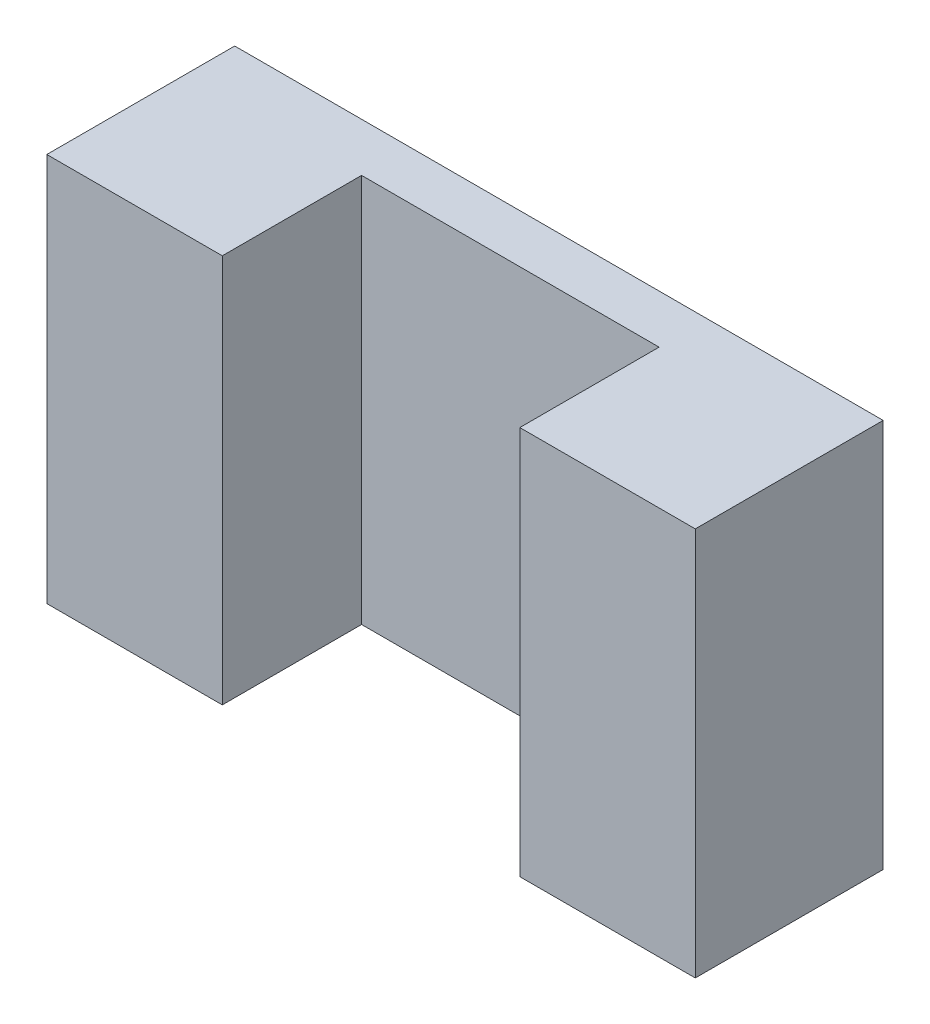
SolidWorks part; units mm, degrees
material "ABS"
ref_plane "Front Plane" through (0, 0, 0) normal (0, 0, 1) x (1, 0, 0)
ref_plane "Top Plane" through (0, 0, 0) normal (0, 1, 0) x (1, 0, 0)
ref_plane "Right Plane" through (0, 0, 0) normal (1, 0, 0) x (0, 0, -1)
sketch "Sketch1" plane through (0, 0, 0) normal (0, 0, 1) x (1, 0, 0)
  line L1 (33.2187, 19.925) -> (-33.2187, 19.925)
  line L2 (33.2187, 19.925) -> (33.2187, -19.925)
  line L3 (33.2187, -19.925) -> (-33.2187, -19.925)
  line L4 (-33.2187, 19.925) -> (-33.2187, -19.925)
  line L5 (33.2187, 19.925) -> (-33.2187, -19.925) construction
  line L6 (33.2187, -19.925) -> (-33.2187, 19.925) construction
  point P0 (0, 0)
  dimension "D1" = 39.85
  dimension "D2" = 66.4375
extrude "Boss-Extrude1" add sketch "Sketch1" along normal blind 20
sketch "Sketch2" plane through (0, 0, 20) normal (0, 0, 1) x (1, 0, 0)
  line L0 (-33.2187, -19.925) -> (33.2187, -19.925) construction
  line L1 (15.24, 19.925) -> (-15.24, 19.925)
  line L2 (15.24, 19.925) -> (15.24, -19.925)
  line L3 (15.24, -19.925) -> (-15.24, -19.925)
  line L4 (-15.24, 19.925) -> (-15.24, -19.925)
  line L5 (15.24, 19.925) -> (-15.24, -19.925) construction
  line L6 (15.24, -19.925) -> (-15.24, 19.925) construction
  point P0 (0, 0)
  dimension "D1" = 30.48
extrude "Cut-Extrude1" cut sketch "Sketch2" against normal blind 15.02
sketch "Sketch3" plane through (0, 0, 20) normal (0, 0, 1) x (1, 0, 0)
  line L1 (-33.2187, 19.925) -> (33.2187, 19.925)
  line L2 (-33.2187, 19.925) -> (-33.2187, -19.925)
  line L3 (-33.2187, -19.925) -> (33.2187, -19.925)
  line L4 (33.2187, 19.925) -> (33.2187, -19.925)
extrude "Cut-Extrude2" cut sketch "Sketch3" against normal blind 0.75
